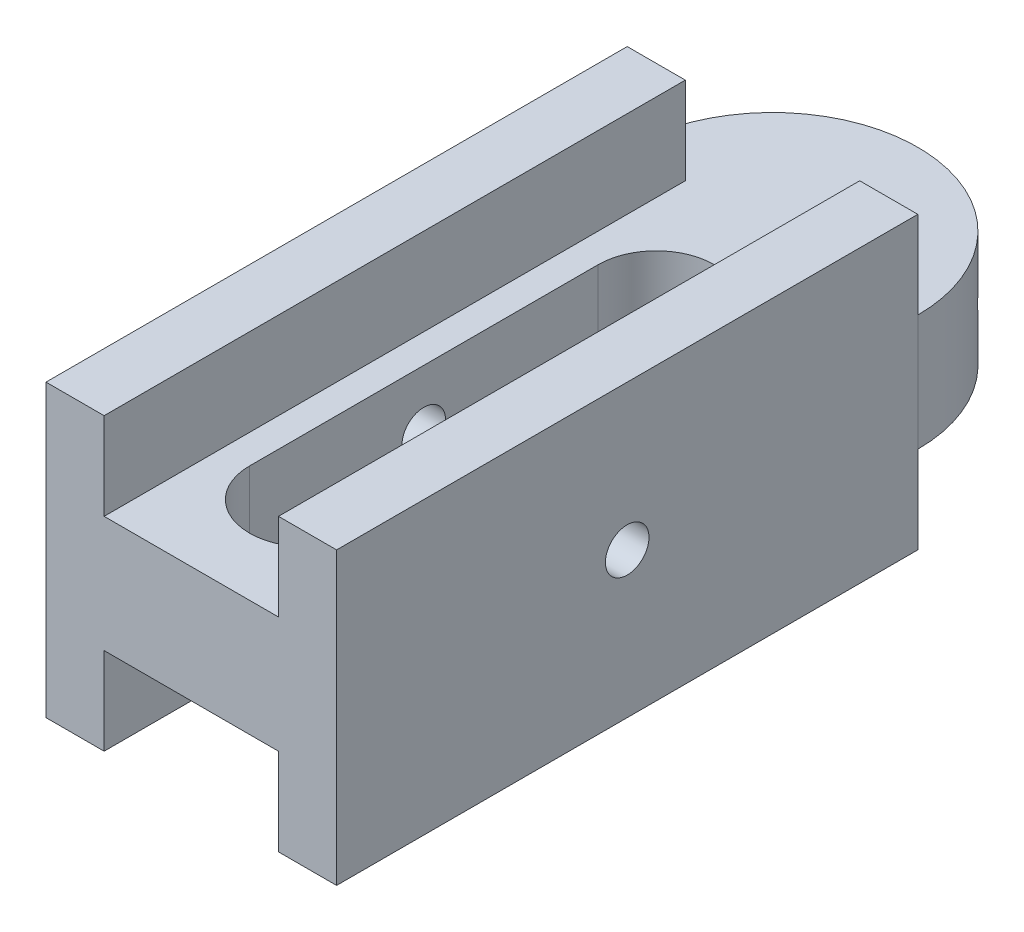
SolidWorks part; units mm, degrees
ref_plane "Front Plane" through (0, 0, 0) normal (0, 0, 1) x (1, 0, 0)
ref_plane "Top Plane" through (0, 0, 0) normal (0, 1, 0) x (1, 0, 0)
ref_plane "Right Plane" through (0, 0, 0) normal (1, 0, 0) x (0, 0, -1)
sketch "Sketch1" plane through (0, 0, 0) normal (0, 0, 1) x (1, 0, 0)
  line L1 (-9.525, 9.525) -> (9.525, 9.525) construction
  line L2 (-9.525, 9.525) -> (-9.525, -9.525) construction
  line L3 (-9.525, -9.525) -> (9.525, -9.525) construction
  line L4 (9.525, 9.525) -> (9.525, -9.525) construction
  line L5 (-9.525, 9.525) -> (9.525, -9.525) construction
  line L6 (-9.525, -9.525) -> (9.525, 9.525) construction
  line L7 (-7.9375, 7.9375) -> (7.9375, 7.9375)
  line L8 (-7.9375, 7.9375) -> (-7.9375, -7.9375)
  line L9 (-7.9375, -7.9375) -> (7.9375, -7.9375)
  line L10 (7.9375, 7.9375) -> (7.9375, -7.9375)
  line L11 (-7.9375, 7.9375) -> (7.9375, -7.9375) construction
  line L12 (-7.9375, -7.9375) -> (7.9375, 7.9375) construction
  point P0 (0, 0)
  point P6 (0, 0)
  dimension "D1" = 19.05
  dimension "D2" = 19.05
  dimension "D3" = 1.5875
extrude "Boss-Extrude1" add sketch "Sketch1" along normal blind 31.75
ref_plane "Plane1" through (0, 0, 0) normal (0, 1, 0) x (1, 0, 0)
sketch "Sketch3" plane through (0, 0, 0) normal (0, 1, 0) x (1, 0, 0)
  line L0 (7.9375, 0) -> (-7.9375, 0) construction
  line L1 (-7.9375, 0) -> (7.9375, 0)
  arc A0 (-7.9375, 0) -> (7.9375, 0) centre (0, 0) cw
extrude "Boss-Extrude3" add sketch "Sketch3" along normal blind 3.175 and the other way blind 3.175
sketch "Sketch4" plane through (7.9375, 0, 0) normal (1, 0, 0) x (0, 0, -1)
  line L0 (-31.75, 0) -> (0, 0) construction
  line L1 (-31.75, -7.9375) -> (-31.75, 7.9375) construction
  line L2 (-15.875, 7.9375) -> (-15.875, -7.9375) construction
  line L3 (-31.75, 7.9375) -> (0, 7.9375) construction
  line L4 (-31.75, -7.9375) -> (0, -7.9375) construction
  line L5 (-31.75, 0) -> (0, 0) construction
  circle A0 centre (-15.875, 0) radius 1.1906
  dimension "D1" = 2.3813
extrude "Cut-Extrude1" cut sketch "Sketch4" against normal through all
sketch "Sketch5" plane through (0, 0, 0) normal (0, 1, 0) x (1, 0, 0)
  line L0 (0, 0) -> (-6.3806, 4.7214)
  line L1 (0, 0) -> (4.7214, 6.3806)
  line L3 (-7.9375, 0) -> (7.9375, 0) construction
  arc A0 (7.9375, 0) -> (-7.9375, 0) centre (0, 0) ccw construction
  dimension "D1" = 53.5
ref_plane "Plane2" through (-6.3806, 0, -4.7214) normal (0.8039, 0, 0.5948) x (0.5948, 0, -0.8039)
sketch "Sketch7" plane through (-6.3806, 0, -4.7214) normal (0.8039, 0, 0.5948) x (0.5948, 0, -0.8039)
  circle A0 centre (0, 0) radius 1.5875
  dimension "D1" = 3.175
ref_plane "Plane3" through (4.7214, 0, -6.3806) normal (0.5948, 0, -0.8039) x (-0.8039, 0, -0.5948)
sketch "Sketch8" plane through (4.7214, 0, -6.3806) normal (0.5948, 0, -0.8039) x (-0.8039, 0, -0.5948)
  circle A0 centre (0, 0) radius 1.5875
  dimension "D1" = 3.175
extrude "Cut-Extrude3" cut sketch "Sketch8" against normal up to vertex (7.9375 mm away) contours A0 up to point (0, 0, 0)
extrude "Cut-Extrude4" cut sketch "Sketch7" along normal up to vertex (7.9375 mm away) contours A0 up to point (0, 0, 0)
sketch "Sketch10" plane through (0, 0, 0) normal (0, 0, -1) x (-1, 0, 0)
  line L0 (-7.9375, 7.9375) -> (7.9375, 7.9375) construction
  line L1 (-4.7625, 7.9375) -> (4.7625, 7.9375)
  line L2 (-4.7625, 7.9375) -> (-4.7625, 3.175)
  line L3 (-4.7625, 3.175) -> (4.7625, 3.175)
  line L4 (4.7625, 7.9375) -> (4.7625, 3.175)
  line L5 (7.9375, 3.175) -> (-7.9375, 3.175) construction
  line L6 (-7.9375, 3.175) -> (-7.9375, 7.9375) construction
  line L7 (7.9375, 7.9375) -> (7.9375, 3.175) construction
  line L8 (-7.9247, 0) -> (7.9375, 0) construction
  line L9 (1.7463, 0) -> (-1.7463, 0) construction
  line L10 (7.9375, -3.175) -> (7.9375, 3.175) construction
  line L11 (4.7625, -7.9375) -> (4.7625, -3.175)
  line L12 (-4.7625, -7.9375) -> (4.7625, -7.9375)
  line L13 (-4.7625, -7.9375) -> (-4.7625, -3.175)
  line L14 (-4.7625, -3.175) -> (4.7625, -3.175)
  dimension "D1" = 3.175
  dimension "D2" = 3.175
extrude "Cut-Extrude5" cut sketch "Sketch10" against normal through all
sketch "Sketch12" plane through (0, 3.175, 0) normal (0, 1, 0) x (1, 0, 0)
  line L0 (0, -31.75) -> (0, 0) construction
  line L2 (0, -25.4) -> (0, -6.35) construction
  line L3 (-3.175, -25.4) -> (-3.175, -6.35)
  line L4 (3.175, -25.4) -> (3.175, -6.35)
  line L5 (4.7625, -31.75) -> (-4.7625, -31.75) construction
  arc A0 (-3.175, -25.4) -> (3.175, -25.4) centre (0, -25.4) ccw
  arc A1 (3.175, -6.35) -> (-3.175, -6.35) centre (0, -6.35) ccw
  point P3 (0, -15.875)
  point P4 (0, -15.875)
  point P5 (0, -15.875)
  point P12 (6.5484, -6.2788)
  dimension "D1" = 6.35
  dimension "D2" = 6.35
extrude "Cut-Extrude6" cut sketch "Sketch12" against normal through all
